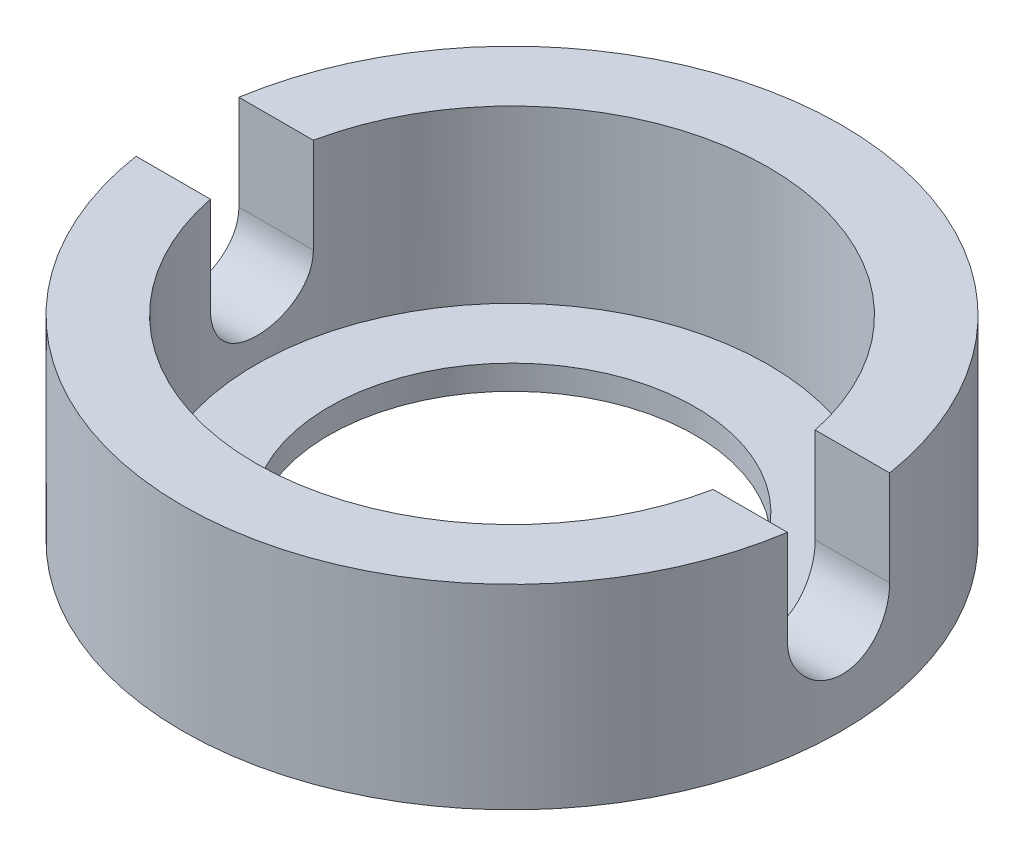
SolidWorks part; units mm, degrees
ref_plane "Piano frontale" through (0, 0, 0) normal (0, 0, 1) x (1, 0, 0)
ref_plane "Piano superiore" through (0, 0, 0) normal (0, 1, 0) x (1, 0, 0)
ref_plane "Piano destro" through (0, 0, 0) normal (1, 0, 0) x (0, 0, -1)
sketch "Schizzo1" plane through (0, 0, 0) normal (0, 1, 0) x (1, 0, 0)
  circle A0 centre (0, 0) radius 13.5
  dimension "D1" = 27
extrude "Estrusione-Estrusione1" add sketch "Schizzo1" along normal blind 8
sketch "Schizzo2" plane through (0, 8, 0) normal (0, 1, 0) x (1, 0, 0)
  circle A0 centre (0, 0) radius 10.5
  dimension "D1" = 21
extrude "Taglio-Estrusione1" cut sketch "Schizzo2" against normal blind 7
sketch "Schizzo3" plane through (0, 1, 0) normal (0, 1, 0) x (1, 0, 0)
  circle A0 centre (0, 0) radius 7.5
  dimension "D1" = 15
extrude "Taglio-Estrusione2" cut sketch "Schizzo3" against normal through all
sketch "Schizzo4" plane through (0, 0, 0) normal (1, 0, 0) x (0, 0, -1)
  line L0 (13.5, 8) -> (-13.5, 8) construction
  line L1 (2.1409, 8) -> (-2.0592, 8)
  line L2 (2.1409, 8) -> (2.1409, 4.1)
  line L4 (-2.0592, 8) -> (-2.0592, 4.1)
  line L5 (0, 0) -> (0.0408, 8) construction
  arc A0 (2.1409, 4.1) -> (-2.0592, 4.1) centre (0.0408, 4.1) cw
  dimension "D1" = 2.1
  dimension "D2" = 3.9
extrude "Taglio-Estrusione4" cut sketch "Schizzo4" against normal through all and the other way through all
sketch "Schizzo5" plane through (0, 0, 0) normal (0, -1, 0) x (1, 0, 0)
  line L0 (0, 13.5) -> (0, -13.5) construction
  circle A0 centre (0, 0) radius 13.5 construction
